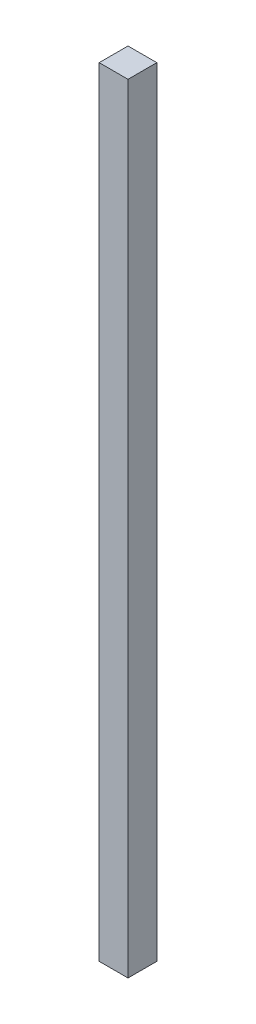
SolidWorks part; units mm, degrees
ref_plane "Front Plane" through (0, 0, 0) normal (0, 0, 1) x (1, 0, 0)
ref_plane "Top Plane" through (0, 0, 0) normal (0, 1, 0) x (1, 0, 0)
ref_plane "Right Plane" through (0, 0, 0) normal (1, 0, 0) x (0, 0, -1)
sketch "Sketch1" plane through (0, 0, 0) normal (0, 1, 0) x (1, 0, 0)
  line L1 (0, 0) -> (25.4, 0)
  line L2 (0, 0) -> (0, 25.4)
  line L3 (0, 25.4) -> (25.4, 25.4)
  line L4 (25.4, 0) -> (25.4, 25.4)
  dimension "D1" = 25.4
  dimension "D2" = 25.4
extrude "Boss-Extrude1" add sketch "Sketch1" along normal blind 685.8
